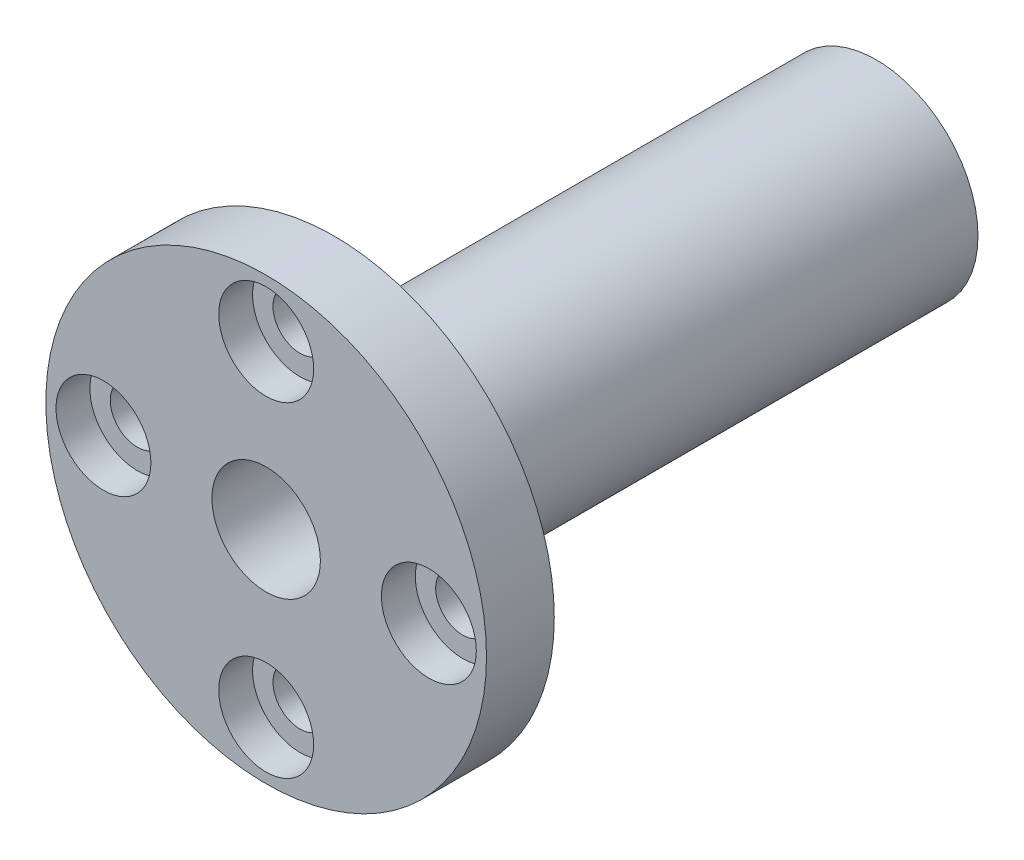
SolidWorks part; units mm, degrees
material "NBR"
ref_plane "前视基准面" through (0, 0, 0) normal (0, 0, 1) x (1, 0, 0)
ref_plane "上视基准面" through (0, 0, 0) normal (0, 1, 0) x (1, 0, 0)
ref_plane "右视基准面" through (0, 0, 0) normal (1, 0, 0) x (0, 0, -1)
other "Configuration Table"
sketch "Sketch1" plane through (0, 0, 0) normal (0, 0, 1) x (1, 0, 0)
  circle A0 centre (0, 0) radius 16.25
  dimension "D1" = 32.5
extrude "Boss-Extrude1" add sketch "Sketch1" along normal blind 5
sketch "Sketch2" plane through (0, 0, 5) normal (0, 0, 1) x (1, 0, 0)
  circle A1 centre (0, 12) radius 3.5
  circle A2 centre (12, 0) radius 3.5
  circle A3 centre (0, -12) radius 3.5
  circle A4 centre (-12, 0) radius 3.5
  point P1 (11.551, 2.1488)
  point P2 (0, 0)
  point P12 (0, 0)
  dimension "D1" = 7
  dimension "D2" = 12
  dimension "D3" = 4
extrude "Cut-Extrude1" cut sketch "Sketch2" against normal blind 2.5
sketch "Sketch3" plane through (0, 0, 0) normal (0, 0, -1) x (-1, 0, 0)
  circle A0 centre (0, 0) radius 7.5
  dimension "D1" = 15
extrude "Boss-Extrude2" add sketch "Sketch3" along normal blind 40
sketch "Sketch4" plane through (0, 0, 5) normal (0, 0, 1) x (1, 0, 0)
  circle A0 centre (0, 0) radius 4
  dimension "D1" = 8
extrude "Cut-Extrude2" cut sketch "Sketch4" against normal through all
sketch "Sketch5" plane through (0, 0, 2.5) normal (0, 0, 1) x (1, 0, 0)
  circle A0 centre (12, 0) radius 2
  circle A1 centre (0, -12) radius 2
  circle A2 centre (-12, 0) radius 2
  circle A3 centre (0, 12) radius 2
  point P3 (0.7191, 1.2485)
  point P4 (12, 0)
  point P12 (0, 0)
  dimension "D1" = 4
  dimension "D2" = 4
extrude "Cut-Extrude3" cut sketch "Sketch5" against normal through all
